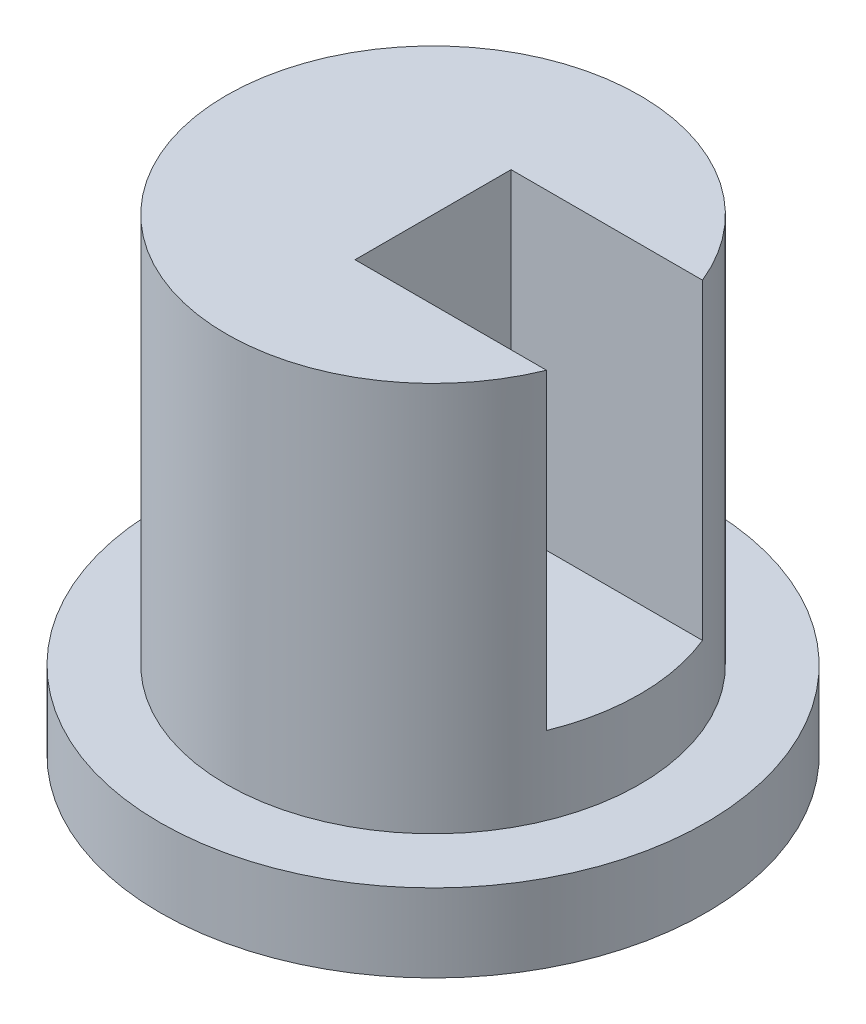
SolidWorks part; units mm, degrees
ref_plane "Alzado" through (0, 0, 0) normal (0, 0, 1) x (1, 0, 0)
ref_plane "Planta" through (0, 0, 0) normal (0, 1, 0) x (1, 0, 0)
ref_plane "Vista lateral" through (0, 0, 0) normal (1, 0, 0) x (0, 0, -1)
sketch "Croquis1" plane through (0, 0, 0) normal (0, 1, 0) x (1, 0, 0)
  circle A0 centre (0, 0) radius 35
  dimension "D1" = 70
extrude "Saliente-Extruir1" add sketch "Croquis1" along normal blind 10
sketch "Croquis2" plane through (0, 10, 0) normal (0, 1, 0) x (1, 0, 0)
  circle A1 centre (0, 0) radius 26.5
  point P0 (0, 0)
  dimension "D1" = 53
extrude "Saliente-Extruir3" add sketch "Croquis2" along normal blind 50 contours A1
sketch "Croquis4" plane through (0, 0, 0) normal (1, 0, 0) x (0, 0, -1)
  line L0 (26.5, 60) -> (-26.5, 60) construction
  line L1 (-10, 60) -> (10, 60)
  line L2 (-10, 60) -> (-10, 20)
  line L3 (-10, 20) -> (10, 20)
  line L4 (10, 60) -> (10, 20)
  line L5 (0, 0) -> (0, 20) construction
  line L6 (-35, 0) -> (35, 0) construction
  dimension "D1" = 20
  dimension "D2" = 40
extrude "Cortar-Extruir2" cut sketch "Croquis4" along normal blind 40
